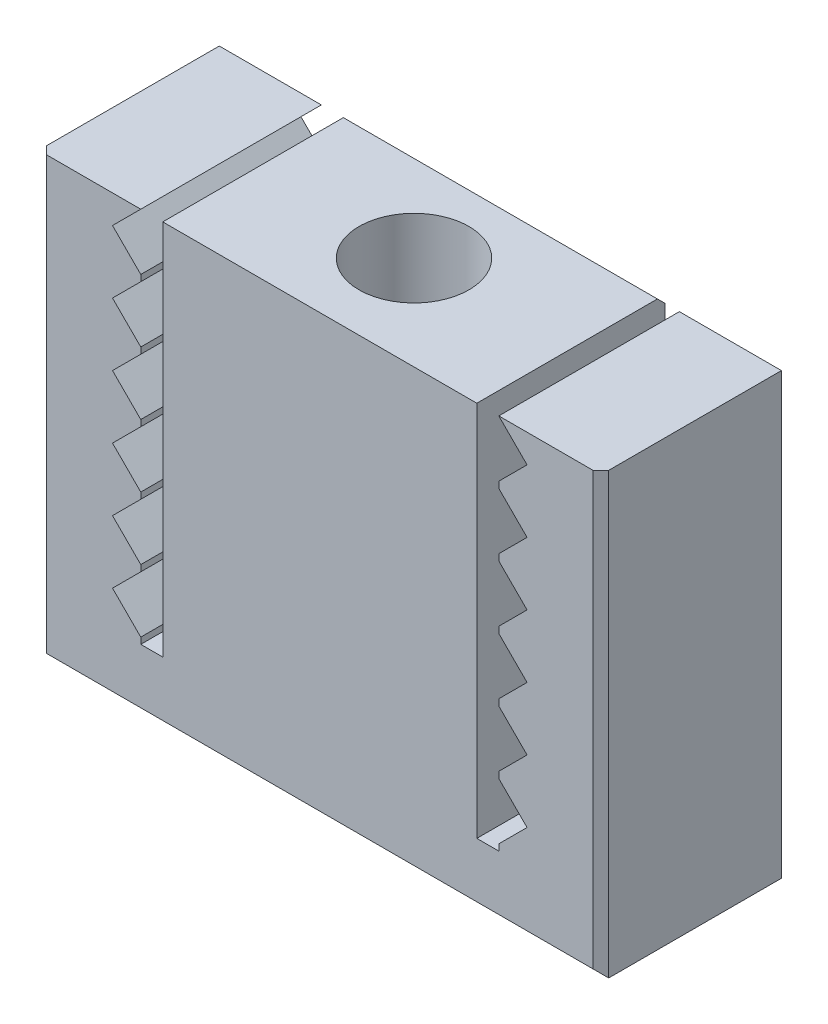
SolidWorks part; units mm, degrees
ref_plane "Front Plane" through (0, 0, 0) normal (0, 0, 1) x (1, 0, 0)
ref_plane "Top Plane" through (0, 0, 0) normal (0, 1, 0) x (1, 0, 0)
ref_plane "Right Plane" through (0, 0, 0) normal (1, 0, 0) x (0, 0, -1)
sketch "Sketch1" plane through (0, 0, 0) normal (0, 0, 1) x (1, 0, 0)
  line L0 (0, 0) -> (0, 16.9576) construction
  line L1 (-8.95, 0) -> (8.95, 0)
  line L2 (8.95, 0) -> (8.95, 14)
  line L3 (8.95, 14) -> (-8.95, 14)
  line L4 (-8.95, 0) -> (-8.95, 14)
  point P8 (0, 14)
  dimension "D1" = 17.9
  dimension "D2" = 14
extrude "Boss-Extrude1" add sketch "Sketch1" along normal blind 6
sketch "Sketch2" plane through (0, 14, 0) normal (0, 1, 0) x (1, 0, 0)
  line L0 (0, 0) -> (0, -6) construction
  line L1 (8.95, -6) -> (-8.95, -6) construction
  circle A0 centre (0, -3) radius 1.75
  dimension "D1" = 3.5
extrude "Cut-Extrude1" cut sketch "Sketch2" against normal through all
sketch "Sketch3" plane through (0, 0, 6) normal (0, 0, 1) x (1, 0, 0)
  line L0 (0, 0) -> (0, 14) construction
  line L1 (-8.95, 0) -> (8.95, 0) construction
  line L2 (8.95, 14) -> (-8.95, 14) construction
  line L3 (5, 14) -> (5, 2)
  line L4 (5.7, 12.2) -> (5.7, 12)
  line L5 (5.7, 14) -> (6.6, 13.1)
  line L6 (6.6, 13.1) -> (5.7, 13.1) construction
  line L7 (5.7, 12.2) -> (6.6, 13.1)
  line L8 (5.7, 12) -> (6.6, 11.1)
  line L9 (5.7, 10.2) -> (6.6, 11.1)
  line L10 (5.7, 10) -> (6.6, 9.1)
  line L11 (5.7, 8.2) -> (6.6, 9.1)
  line L12 (5.7, 8) -> (6.6, 7.1)
  line L13 (5.7, 6.2) -> (6.6, 7.1)
  line L14 (5.7, 6) -> (6.6, 5.1)
  line L15 (5.7, 4.2) -> (6.6, 5.1)
  line L16 (5.7, 4) -> (6.6, 3.1)
  line L17 (5.7, 2.2) -> (6.6, 3.1)
  line L20 (5, 14) -> (5.7, 14)
  line L22 (5.7, 14) -> (5.7, 13.1) construction
  line L23 (5.7, 13.1) -> (5.7, 12.2) construction
  line L24 (5.7, 12) -> (5.7, 10.2) construction
  line L25 (5.7, 10.2) -> (5.7, 10)
  line L26 (5.7, 10) -> (5.7, 8.2) construction
  line L27 (5.7, 8.2) -> (5.7, 8)
  line L28 (5.7, 8) -> (5.7, 6.2) construction
  line L29 (5.7, 6.2) -> (5.7, 6)
  line L30 (5.7, 6) -> (5.7, 4.2) construction
  line L31 (5.7, 4.2) -> (5.7, 4)
  line L32 (5.7, 4) -> (5.7, 2.2) construction
  line L33 (5.7, 2.2) -> (5.7, 2)
  line L37 (-5.7, 4) -> (-5.7, 2.2) construction
  line L38 (-5.7, 6) -> (-5.7, 4.2) construction
  line L39 (-5.7, 8) -> (-5.7, 6.2) construction
  line L40 (-5.7, 10) -> (-5.7, 8.2) construction
  line L41 (-5.7, 12) -> (-5.7, 10.2) construction
  line L42 (-5.7, 13.1) -> (-5.7, 12.2) construction
  line L43 (-5.7, 14) -> (-5.7, 13.1) construction
  line L44 (-6.6, 13.1) -> (-5.7, 13.1) construction
  line L46 (-5.7, 2.2) -> (-5.7, 2)
  line L47 (-5.7, 4.2) -> (-5.7, 4)
  line L48 (-5.7, 6.2) -> (-5.7, 6)
  line L49 (-5.7, 8.2) -> (-5.7, 8)
  line L50 (-5.7, 10.2) -> (-5.7, 10)
  line L52 (-5, 14) -> (-5.7, 14)
  line L55 (-5.7, 2.2) -> (-6.6, 3.1)
  line L56 (-5.7, 4) -> (-6.6, 3.1)
  line L57 (-5.7, 4.2) -> (-6.6, 5.1)
  line L58 (-5.7, 6) -> (-6.6, 5.1)
  line L59 (-5.7, 6.2) -> (-6.6, 7.1)
  line L60 (-5.7, 8) -> (-6.6, 7.1)
  line L61 (-5.7, 8.2) -> (-6.6, 9.1)
  line L62 (-5.7, 10) -> (-6.6, 9.1)
  line L63 (-5.7, 10.2) -> (-6.6, 11.1)
  line L64 (-5.7, 12) -> (-6.6, 11.1)
  line L65 (-5.7, 12.2) -> (-6.6, 13.1)
  line L66 (-5.7, 14) -> (-6.6, 13.1)
  line L67 (-5.7, 12.2) -> (-5.7, 12)
  line L68 (-5, 14) -> (-5, 2)
  line L69 (5.7, 2) -> (5, 2)
  line L72 (-5, 2) -> (-5.7, 2)
  line L73 (5.7, 2) -> (6.6, 1.1)
  line L74 (5.7, 0.2) -> (6.6, 1.1)
  point P7 (-5.1179, 2)
  point P62 (0, 0)
  dimension "D1" = 0.7
  dimension "D2" = 1.6
  dimension "D3" = 90
  dimension "D4" = 5
  dimension "D6" = 2
  dimension "D7" = 2
  dimension "D5" = 7
extrude "Cut-Extrude2" cut sketch "Sketch3" against normal blind 6
chamfer "Chamfer1" distance 0.25 angle 45 9 edges at (0, 14, 0) (8.95, 7, 6) (-7.325, 14, 0) (7.325, 14, 0) (8.95, 7, 0) (0, 0, 0) (-8.95, 7, 0) (-8.95, 7, 6) (0, 0, 6)
